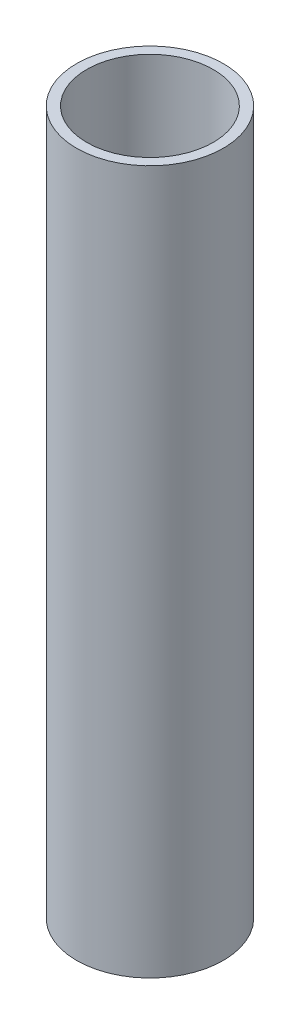
SolidWorks part; units mm, degrees
material "Epoxy, Unfilled"
ref_plane "Front Plane" through (0, 0, 0) normal (0, 0, 1) x (1, 0, 0)
ref_plane "Top Plane" through (0, 0, 0) normal (0, 1, 0) x (1, 0, 0)
ref_plane "Right Plane" through (0, 0, 0) normal (1, 0, 0) x (0, 0, -1)
sketch "Sketch2" plane through (0, 0, 0) normal (0, 1, 0) x (1, 0, 0)
  circle A0 centre (0, 0) radius 58.293
  circle A1 centre (0, 0) radius 50.2539
extrude "Boss-Extrude1" add sketch "Sketch2" along normal blind 558.8
